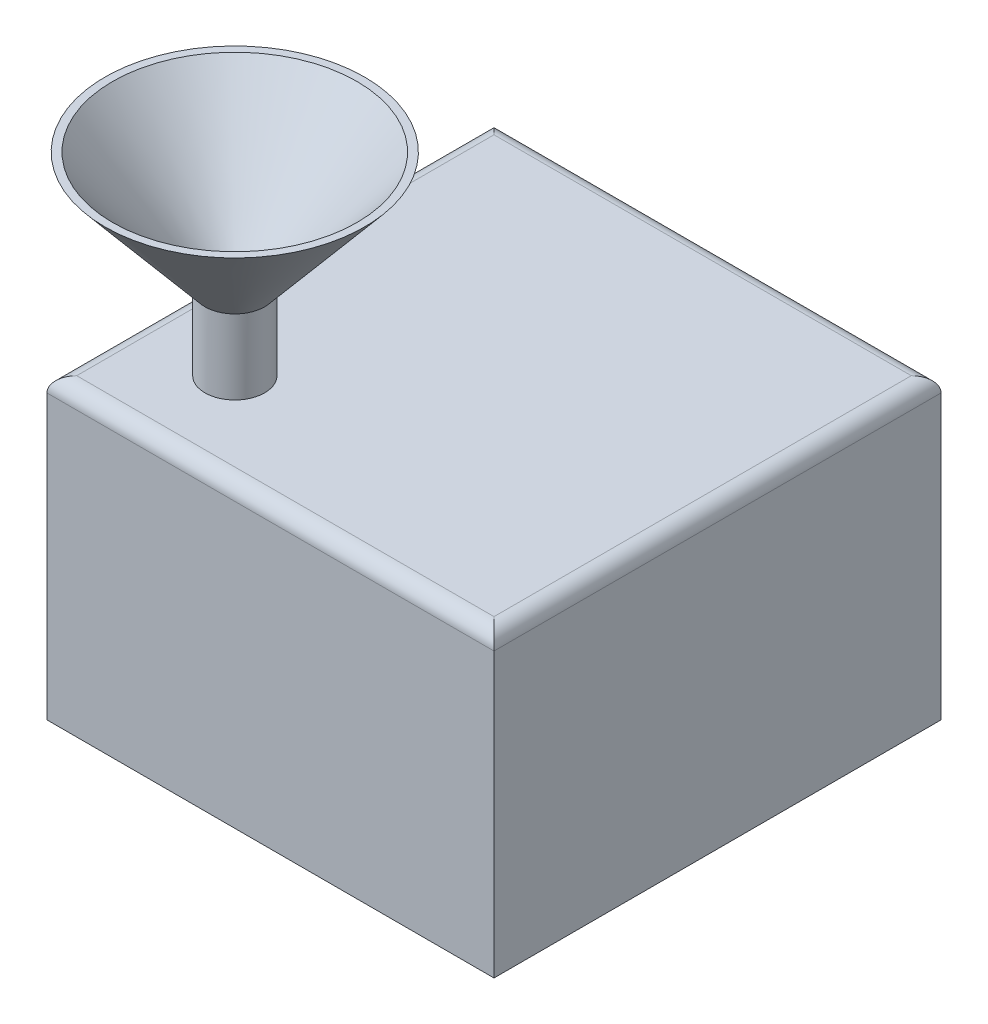
SolidWorks part; units mm, degrees
ref_plane "Front Plane" through (0, 0, 0) normal (0, 0, 1) x (1, 0, 0)
ref_plane "Top Plane" through (0, 0, 0) normal (0, 1, 0) x (1, 0, 0)
ref_plane "Right Plane" through (0, 0, 0) normal (1, 0, 0) x (0, 0, -1)
sketch "Sketch1" plane through (0, 0, 0) normal (0, 1, 0) x (1, 0, 0)
  line L1 (-150, -150) -> (150, -150)
  line L2 (-150, -150) -> (-150, 150)
  line L3 (-150, 150) -> (150, 150)
  line L4 (150, -150) -> (150, 150)
  line L5 (-150, -150) -> (150, 150) construction
  line L6 (-150, 150) -> (150, -150) construction
  point P0 (0, 0)
extrude "Boss-Extrude1" add sketch "Sketch1" along normal blind 200
fillet "Fillet1" radius 10 4 edges at (0, 200, 150) (-150, 200, 0) (0, 200, -150) (150, 200, 0)
sketch "Sketch2" plane through (0, 200, 0) normal (0, 1, 0) x (1, 0, 0)
  line L0 (-140, -140) -> (-86.967, -86.967)
  circle A0 centre (-86.967, -86.967) radius 20
  circle A1 centre (-86.967, -86.967) radius 15
extrude "Boss-Extrude2" add sketch "Sketch2" along normal blind 50
sketch "Sketch3" plane through (0, 250, 0) normal (0, 1, 0) x (1, 0, 0)
  circle A1 centre (-86.967, -86.967) radius 20
extrude "Boss-Extrude3" add sketch "Sketch3" along normal blind 80 draft 40 draft outward yes
sketch "Sketch4" plane through (0, 330, 0) normal (0, 1, 0) x (1, 0, 0)
  circle A1 centre (-86.967, -86.967) radius 82
extrude "Cut-Extrude1" cut sketch "Sketch4" against normal blind 80 draft 40
